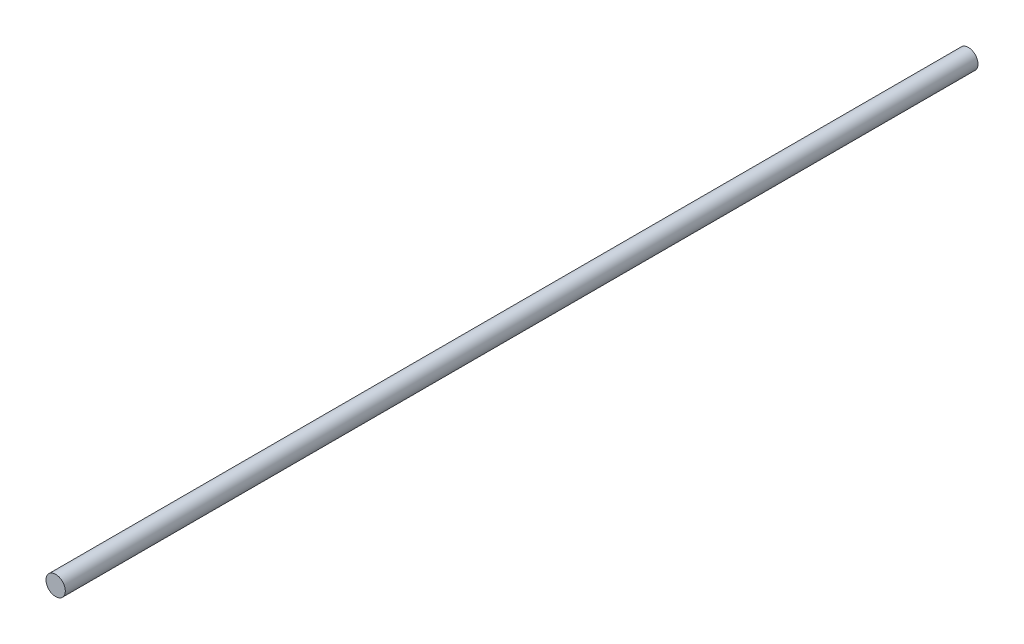
SolidWorks part; units mm, degrees
ref_plane "前视基准面" through (0, 0, 0) normal (0, 0, 1) x (1, 0, 0)
ref_plane "上视基准面" through (0, 0, 0) normal (0, 1, 0) x (1, 0, 0)
ref_plane "右视基准面" through (0, 0, 0) normal (1, 0, 0) x (0, 0, -1)
sketch "草图1" plane through (0, 0, 0) normal (0, 0, 1) x (1, 0, 0)
  circle A0 centre (0, 0) radius 2
extrude "凸台-拉伸1" add sketch "草图1" along normal blind 189
cosmetic thread "装饰螺纹线1" parameters "D1"=16, "D2"=3.242
